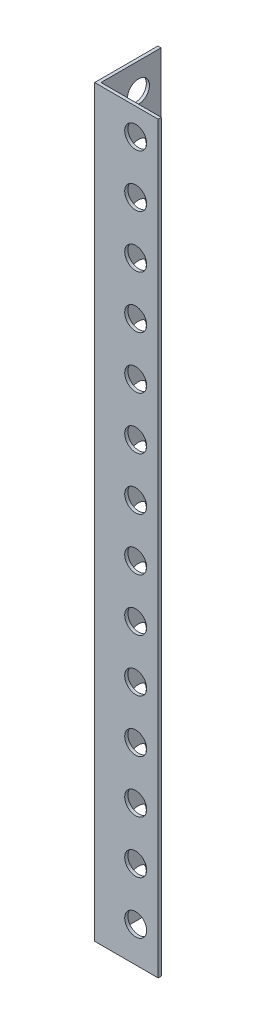
SolidWorks part; units mm, degrees
ref_plane "Front Plane" through (0, 0, 0) normal (0, 0, 1) x (1, 0, 0)
ref_plane "Top Plane" through (0, 0, 0) normal (0, 1, 0) x (1, 0, 0)
ref_plane "Right Plane" through (0, 0, 0) normal (1, 0, 0) x (0, 0, -1)
sketch "Sketch1" plane through (0, 0, 0) normal (0, 1, 0) x (1, 0, 0)
  line L0 (0, 0) -> (31.0261, 0)
  line L1 (31.0261, 0) -> (31.0261, 1.54)
  line L2 (31.0261, 1.54) -> (1.54, 1.54)
  line L3 (1.54, 1.54) -> (1.54, 30.861)
  line L4 (1.54, 30.861) -> (0, 30.861)
  line L5 (0, 30.861) -> (0, 0)
  dimension "D1" = 31.0261
  dimension "D2" = 30.861
  dimension "D3" = 1.54
  dimension "D4" = 1.54
extrude "Boss-Extrude2" add sketch "Sketch1" along normal blind 363.031
sketch "Sketch2" plane through (0, 0, 0) normal (-1, 0, 0) x (0, 0, 1)
  line L0 (-19.861, 363.031) -> (-19.861, 350.031) construction
  line L2 (-30.861, 363.031) -> (0, 363.031) construction
  line L3 (-30.861, 363.031) -> (-30.861, 0) construction
  circle A0 centre (-19.861, 350.031) radius 5.35
  dimension "D2" = 10.7
  dimension "D1" = 13
  dimension "D3" = 11
extrude "Cut-Extrude1" cut sketch "Sketch2" against normal through all
sketch "Sketch3" plane through (0, 0, 0) normal (0, 0, 1) x (1, 0, 0)
  line L0 (20.0261, 363.031) -> (20.0261, 350.031) construction
  line L2 (0, 363.031) -> (31.0261, 363.031) construction
  line L3 (31.0261, 363.031) -> (31.0261, 0) construction
  circle A0 centre (20.0261, 350.031) radius 5.35
  dimension "D2" = 10.7
  dimension "D1" = 13
  dimension "D3" = 11
extrude "Cut-Extrude2" cut sketch "Sketch3" against normal through all
pattern_linear "LPattern2" count 15 spacing 25.6 along (0, -1, 0) of "Cut-Extrude1", "Cut-Extrude2"
